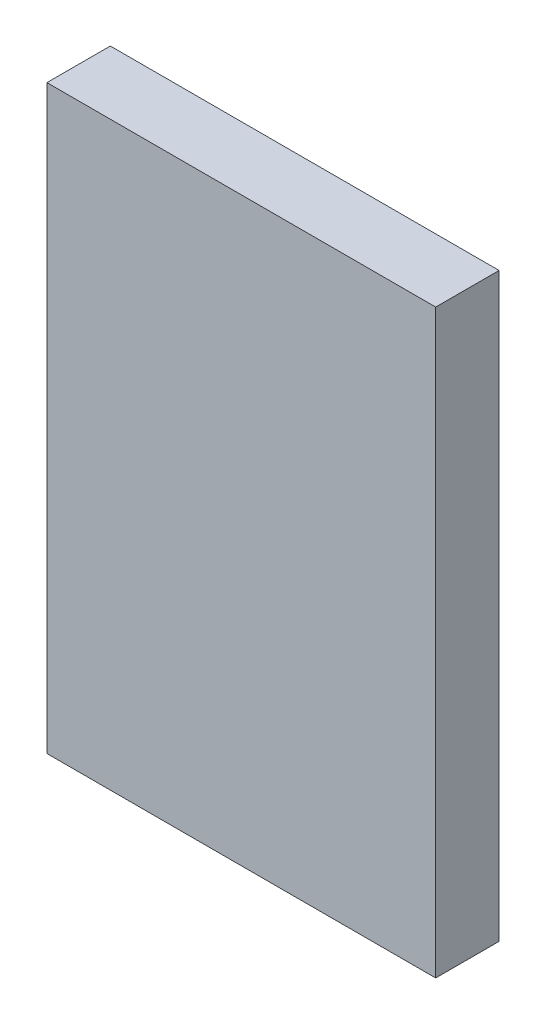
SolidWorks part; units mm, degrees
material "ABS"
ref_plane "Front Plane" through (0, 0, 0) normal (0, 0, 1) x (1, 0, 0)
ref_plane "Top Plane" through (0, 0, 0) normal (0, 1, 0) x (1, 0, 0)
ref_plane "Right Plane" through (0, 0, 0) normal (1, 0, 0) x (0, 0, -1)
sketch "Sketch1" plane through (0, 0, 0) normal (0, 0, 1) x (1, 0, 0)
  line L1 (-27.6, -41.25) -> (27.6, -41.25)
  line L2 (-27.6, -41.25) -> (-27.6, 41.25)
  line L3 (-27.6, 41.25) -> (27.6, 41.25)
  line L4 (27.6, -41.25) -> (27.6, 41.25)
  line L5 (-27.6, -41.25) -> (27.6, 41.25) construction
  line L6 (-27.6, 41.25) -> (27.6, -41.25) construction
  point P0 (0, 0)
  dimension "D1" = 55.2
  dimension "D2" = 82.5
extrude "Boss-Extrude1" add sketch "Sketch1" along normal blind 9
